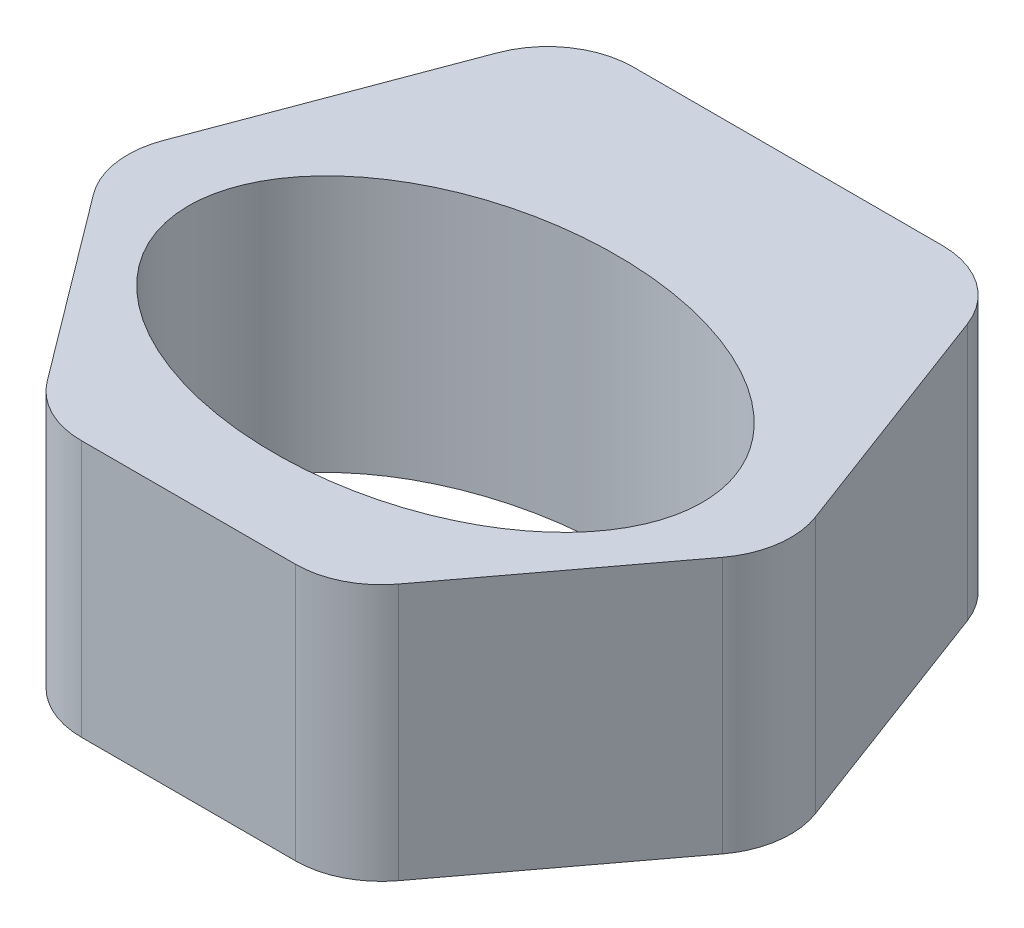
SolidWorks part; units mm, degrees
ref_plane "Front Plane" through (0, 0, 0) normal (0, 0, 1) x (1, 0, 0)
ref_plane "Top Plane" through (0, 0, 0) normal (0, 1, 0) x (1, 0, 0)
ref_plane "Right Plane" through (0, 0, 0) normal (1, 0, 0) x (0, 0, -1)
sketch "Sketch1" plane through (0, 0, 0) normal (0, 1, 0) x (1, 0, 0)
  line L0 (25, 40) -> (-25, 40)
  line L1 (0, 20) -> (0, 40) construction
  line L2 (-25, 40) -> (-40, 0)
  line L3 (-40, 0) -> (-17.5, -30)
  line L4 (-17.5, -30) -> (17.5, -30)
  line L5 (25, 40) -> (40, 0)
  line L6 (40, 0) -> (17.5, -30)
  ellipse E0 centre (0, 0) end of major axis (-30, 0) minor radius 20
  point P16 (0, -30)
  dimension "D1" = 60
  dimension "D2" = 40
  dimension "D3" = 50
  dimension "D4" = 20
  dimension "D5" = 35
  dimension "D6" = 10
  dimension "D7" = 10
extrude "Boss-Extrude1" add sketch "Sketch1" along normal blind 30
fillet "Fillet1" radius 10 6 edges at (-17.5, 15, 30) (17.5, 15, 30) (40, 15, 0) (-40, 15, 0) (-25, 15, -40) (25, 15, -40)
